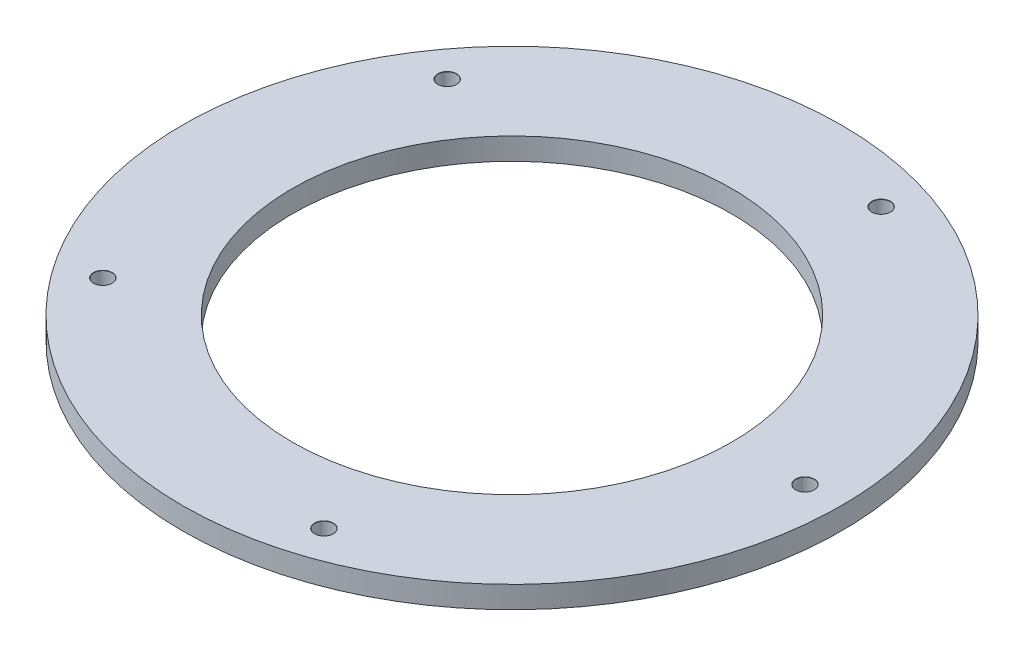
SolidWorks part; units mm, degrees
ref_plane "前视基准面" through (0, 0, 0) normal (0, 0, 1) x (1, 0, 0)
ref_plane "上视基准面" through (0, 0, 0) normal (0, 1, 0) x (1, 0, 0)
ref_plane "右视基准面" through (0, 0, 0) normal (1, 0, 0) x (0, 0, -1)
other "Configuration Table"
sketch "草图1" plane through (0, 0, 0) normal (0, 1, 0) x (1, 0, 0)
  circle A0 centre (0, 0) radius 45
  dimension "D1" = 90
extrude "凸台-拉伸1" add sketch "草图1" along normal blind 3
sketch "草图5" plane through (0, 3, 0) normal (0, 1, 0) x (1, 0, 0)
  circle A0 centre (0, 0) radius 30
  dimension "D1" = 60
extrude "切除-拉伸1" cut sketch "草图5" against normal through all both and the other way through all
sketch "草图7" plane through (0, 3, 0) normal (0, 1, 0) x (1, 0, 0)
  line L0 (0, 0) -> (45, 0) construction
  circle A0 centre (0, 0) radius 45 construction
  circle A1 centre (0, 0) radius 36 construction
  circle A2 centre (40, 0) radius 1.5
  circle A3 centre (12.3607, -38.0423) radius 1.5
  circle A4 centre (-32.3607, -23.5114) radius 1.5
  circle A5 centre (-32.3607, 23.5114) radius 1.5
  circle A6 centre (12.3607, 38.0423) radius 1.5
  point P6 (40, 0)
  point P13 (12.3607, -38.0423)
  point P15 (-32.3607, -23.5114)
  point P17 (-32.3607, 23.5114)
  point P19 (12.3607, 38.0423)
  point P21 (0, 0)
  dimension "D1" = 72
  dimension "D3" = 3
  dimension "D2" = 5
  dimension "D4" = 5
hole_wizard "M3 螺纹孔的螺纹孔钻头2" positions "草图7" profile "草图13" hole size "M3" standard "GB" end condition through all
sketch "草图13" plane through (0, 3, 0) normal (1, 0, 0) x (0, 0, 1)
  line L0 (0, 0) -> (0, 3)
  line L1 (0, 3) -> (1.25, 3)
  line L2 (1.25, 3) -> (1.25, 0.025)
  line L3 (1.25, 0.025) -> (1.275, 0)
  line L5 (1.275, 0) -> (0, 0)
  line L6 (-1.25, 0.025) -> (-1.275, 0) construction
  line L11 (0, -6.35) -> (0, 107.95) construction
  dimension "通孔孔直径" = 2.5
  dimension "通孔孔深度" = 3
  dimension "近端锥形沉头孔直径" = 2.55
  dimension "近端锥形沉头孔角度" = 90
cosmetic thread "装饰螺纹线1" parameters "D2"=3
cosmetic thread "装饰螺纹线2" parameters "D2"=3
cosmetic thread "装饰螺纹线3" parameters "D2"=3
cosmetic thread "装饰螺纹线4" parameters "D2"=3
cosmetic thread "装饰螺纹线5" parameters "D2"=3
